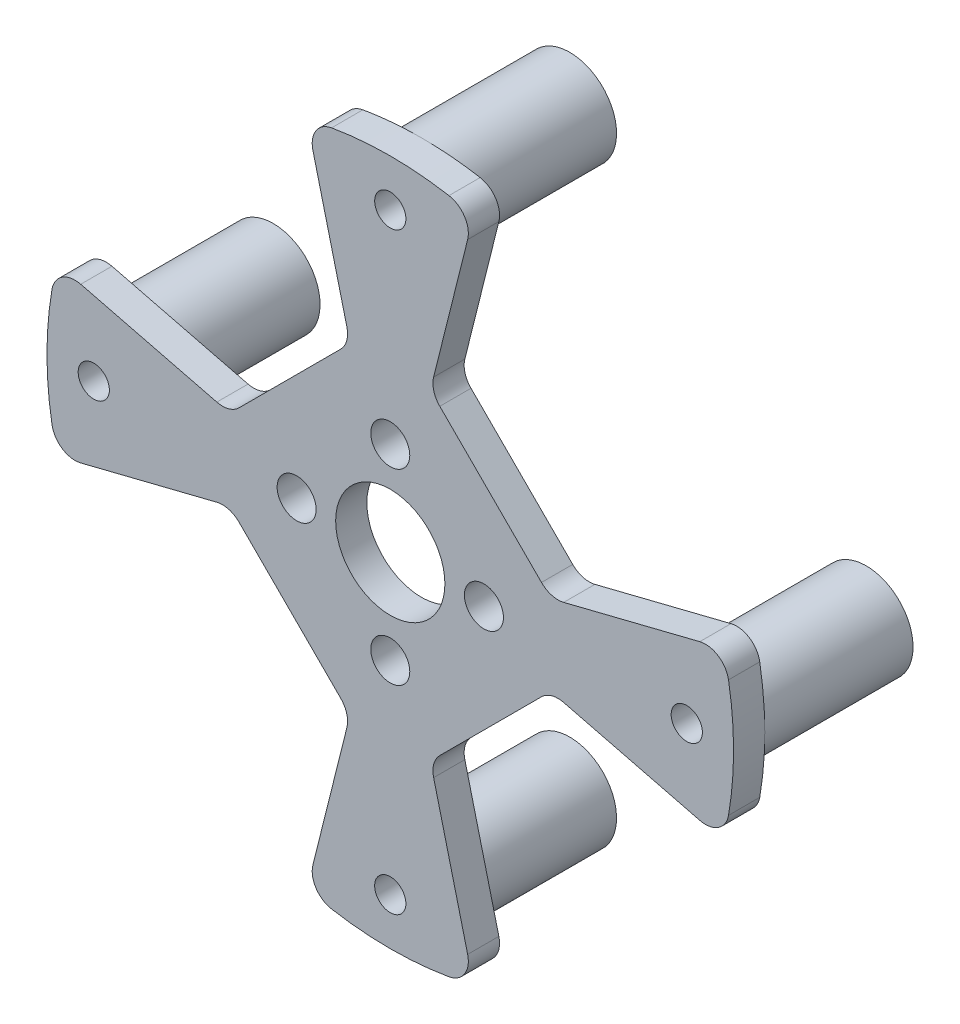
SolidWorks part; units mm, degrees
ref_plane "前视基准面" through (0, 0, 0) normal (0, 0, 1) x (1, 0, 0)
ref_plane "上视基准面" through (0, 0, 0) normal (0, 1, 0) x (1, 0, 0)
ref_plane "右视基准面" through (0, 0, 0) normal (1, 0, 0) x (0, 0, -1)
sketch "草图1" plane through (0, 0, 0) normal (0, 0, 1) x (1, 0, 0)
  circle A0 centre (0, 0) radius 22
extrude "凸台-拉伸1" add sketch "草图1" along normal blind 2
sketch "草图3" plane through (0, 0, 0) normal (0, 0, -1) x (-1, 0, 0)
  line L0 (0, -6) -> (0, 6) construction
  line L1 (6, 6) -> (-6, 6) construction
  line L2 (6, 6) -> (6, -6) construction
  line L3 (6, -6) -> (-6, -6) construction
  line L4 (-6, 6) -> (-6, -6) construction
  line L5 (6, 6) -> (-6, -6) construction
  line L6 (6, -6) -> (-6, 6) construction
  circle A3 centre (6, 0) radius 1.25
  point P0 (0, 0)
extrude "切除-拉伸1" cut sketch "草图3" against normal blind 3
sketch "草图4" plane through (0, 0, 0) normal (0, 0, -1) x (-1, 0, 0)
  circle A0 centre (0, 0) radius 3.5
extrude "切除-拉伸2" cut sketch "草图4" against normal blind 3
sketch "草图6" plane through (0, 0, 0) normal (0, 0, -1) x (-1, 0, 0)
  line L0 (0, -7.5) -> (0, -22) construction
  circle A1 centre (0, 0) radius 22 construction
  circle A2 centre (0, -19) radius 3
extrude "凸台-拉伸3" add sketch "草图6" along normal blind 9.5
sketch "草图8" plane through (0, 0, -9.5) normal (0, 0, -1) x (-1, 0, 0)
  circle A0 centre (0, -19) radius 1
extrude "切除-拉伸4" cut sketch "草图8" along a picked direction on the side against the normal blind 11.5
sketch "草图7" plane through (0, 0, 0) normal (0, 0, -1) x (-1, 0, 0)
  line L0 (-6, 0) -> (0, 6) construction
  line L1 (0, 0) -> (-6, 1.5) construction
  line L2 (-6, 1.5) -> (-25.0731, 6.2683) construction
  line L3 (0, 0) -> (-1.5, 6) construction
  line L4 (-1.5, 6) -> (-6.7018, 26.8073) construction
  line L5 (-2.5727, 10.291) -> (-10.291, 2.5727)
  line L6 (-7.6282, 30.5128) -> (-30.5128, 7.6282)
  line L7 (-10.291, 2.5727) -> (-30.5128, 7.6282)
  line L8 (-7.6282, 30.5128) -> (-2.5727, 10.291)
extrude "切除-拉伸3" cut sketch "草图7" against normal blind 6
pattern_circular "阵列(圆周)1" count 4 over 360 about axis through (0, 0, 0) along (0, 0, 1) of "凸台-拉伸3", "切除-拉伸4", "切除-拉伸1", "切除-拉伸3"
fillet "圆角2" radius 1.5 8 edges at (-21.3431, 5.3358, 1) (-21.3431, -5.3358, 1) (-5.3358, -21.3431, 1) (5.3358, -21.3431, 1) (21.3431, -5.3358, 1) (21.3431, 5.3358, 1) (5.3358, 21.3431, 1) (-5.3358, 21.3431, 1)
fillet "圆角3" radius 1.5 8 edges at (-2.5727, -10.291, 1) (-10.291, -2.5727, 1) (2.5727, -10.291, 1) (10.291, -2.5727, 1) (10.291, 2.5727, 1) (2.5727, 10.291, 1) (-2.5727, 10.291, 1) (-10.291, 2.5727, 1)
